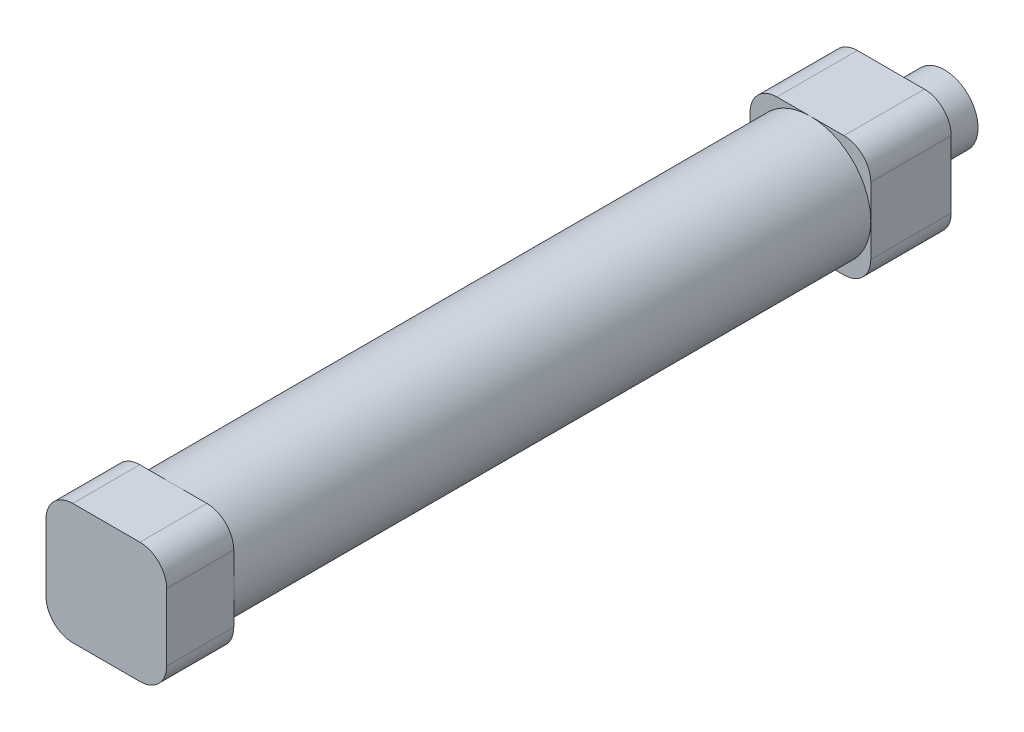
SolidWorks part; units mm, degrees
material "合金钢"
ref_plane "前视基准面" through (0, 0, 0) normal (0, 0, 1) x (1, 0, 0)
ref_plane "上视基准面" through (0, 0, 0) normal (0, 1, 0) x (1, 0, 0)
ref_plane "右视基准面" through (0, 0, 0) normal (1, 0, 0) x (0, 0, -1)
sketch "草图1" plane through (0, 0, 0) normal (0, 0, 1) x (1, 0, 0)
  circle A0 centre (0, 0) radius 9
  circle A1 centre (0, 0) radius 8
  dimension "D1" = 18
  dimension "D2" = 16
extrude "凸台-拉伸1" add sketch "草图1" along normal blind 95
sketch "草图2" plane through (0, 0, 95) normal (0, 0, 1) x (1, 0, 0)
  line L1 (-5, -9) -> (5, -9)
  line L2 (-9, -5) -> (-9, 5)
  line L3 (-5, 9) -> (5, 9)
  line L4 (9, -5) -> (9, 5)
  line L5 (-9, -9) -> (9, 9) construction
  line L6 (-9, 9) -> (9, -9) construction
  arc A0 (-5, 9) -> (-9, 5) centre (-5, 5) ccw
  arc A1 (9, 5) -> (5, 9) centre (5, 5) ccw
  arc A2 (9, -5) -> (5, -9) centre (5, -5) cw
  arc A3 (-9, -5) -> (-5, -9) centre (-5, -5) ccw
  point P0 (0, 0)
  dimension "D3" = 4
  dimension "D4" = 4
  dimension "D5" = 4
  dimension "D6" = 4
  dimension "D1" = 18
  dimension "D2" = 18
extrude "凸台-拉伸2" add sketch "草图2" along normal blind 10
sketch "草图3" plane through (0, 0, 0) normal (0, 0, -1) x (-1, 0, 0)
  line L1 (-5, -9) -> (5, -9)
  line L2 (-9, -5) -> (-9, 5)
  line L3 (-5, 9) -> (5, 9)
  line L4 (9, -5) -> (9, 5)
  line L5 (-9, -9) -> (9, 9) construction
  line L6 (-9, 9) -> (9, -9) construction
  arc A0 (-9, -5) -> (-5, -9) centre (-5, -5) ccw
  arc A1 (5, -9) -> (9, -5) centre (5, -5) ccw
  arc A2 (9, 5) -> (5, 9) centre (5, 5) ccw
  arc A3 (-5, 9) -> (-9, 5) centre (-5, 5) ccw
  point P0 (0, 0)
  dimension "D3" = 4
  dimension "D1" = 18
  dimension "D2" = 18
extrude "凸台-拉伸3" add sketch "草图3" along normal blind 12
sketch "草图4" plane through (0, 0, -12) normal (0, 0, -1) x (-1, 0, 0)
  circle A0 centre (0, 0) radius 5
extrude "凸台-拉伸4" add sketch "草图4" along normal blind 8
sketch "草图5" plane through (0, 0, -20) normal (0, 0, -1) x (-1, 0, 0)
  circle A0 centre (0, 0) radius 2.5
extrude "切除-拉伸1" cut sketch "草图5" against normal blind 38
sketch "草图6" plane through (-9, 0, 0) normal (-1, 0, 0) x (0, 0, 1)
  line L0 (0, -9) -> (0, 9) construction
  circle A0 centre (-4, 0) radius 2
  circle A1 centre (99, 0) radius 1.9805
  dimension "D1" = 4
  dimension "D2" = 4
extrude "切除-拉伸3" cut sketch "草图6" against normal blind 3
